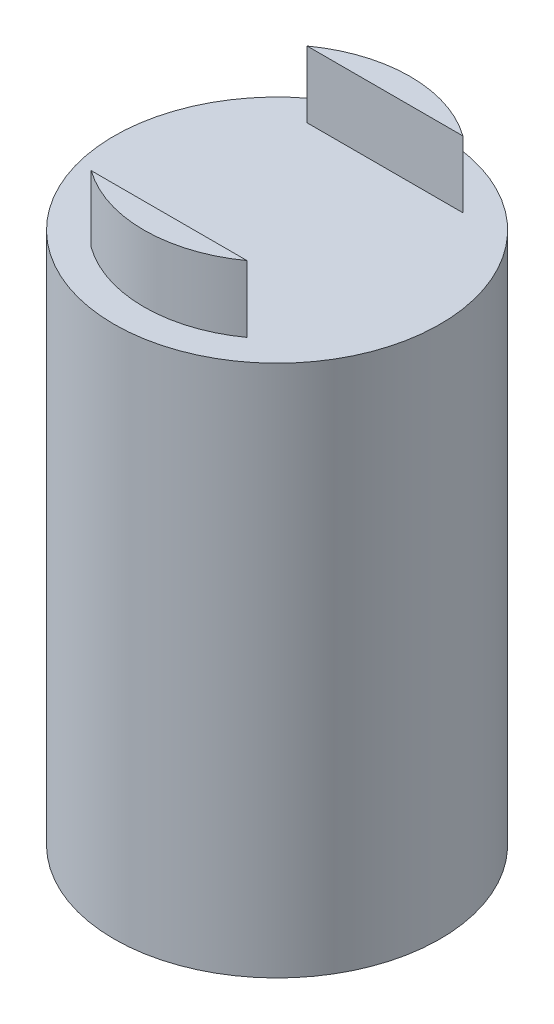
SolidWorks part; units mm, degrees
ref_plane "Front Plane" through (0, 0, 0) normal (0, 0, 1) x (1, 0, 0)
ref_plane "Top Plane" through (0, 0, 0) normal (0, 1, 0) x (1, 0, 0)
ref_plane "Right Plane" through (0, 0, 0) normal (1, 0, 0) x (0, 0, -1)
sketch "Sketch1" plane through (0, 0, 0) normal (0, 1, 0) x (1, 0, 0)
  circle A0 centre (0, 0) radius 31.115
  dimension "D1" = 62.23
extrude "Boss-Extrude4" add sketch "Sketch1" along normal blind 101.6 separate body contours A0
sketch "Sketch4" plane through (0, 101.6, 0) normal (0, 1, 0) x (1, 0, 0)
  line L0 (-14.859, 20.6002) -> (14.859, 20.6002)
  line L5 (0, 0) -> (-11.6386, 0) construction
  line L6 (-14.859, -20.6002) -> (14.859, -20.6002)
  circle A0 centre (0, 0) radius 25.4
  point P4 (0, 20.6002)
  dimension "D1" = 50.8
  dimension "D2" = 29.718
extrude "Boss-Extrude6" add sketch "Sketch4" along normal blind 12.7 contours L0 A0 | L6 A0
